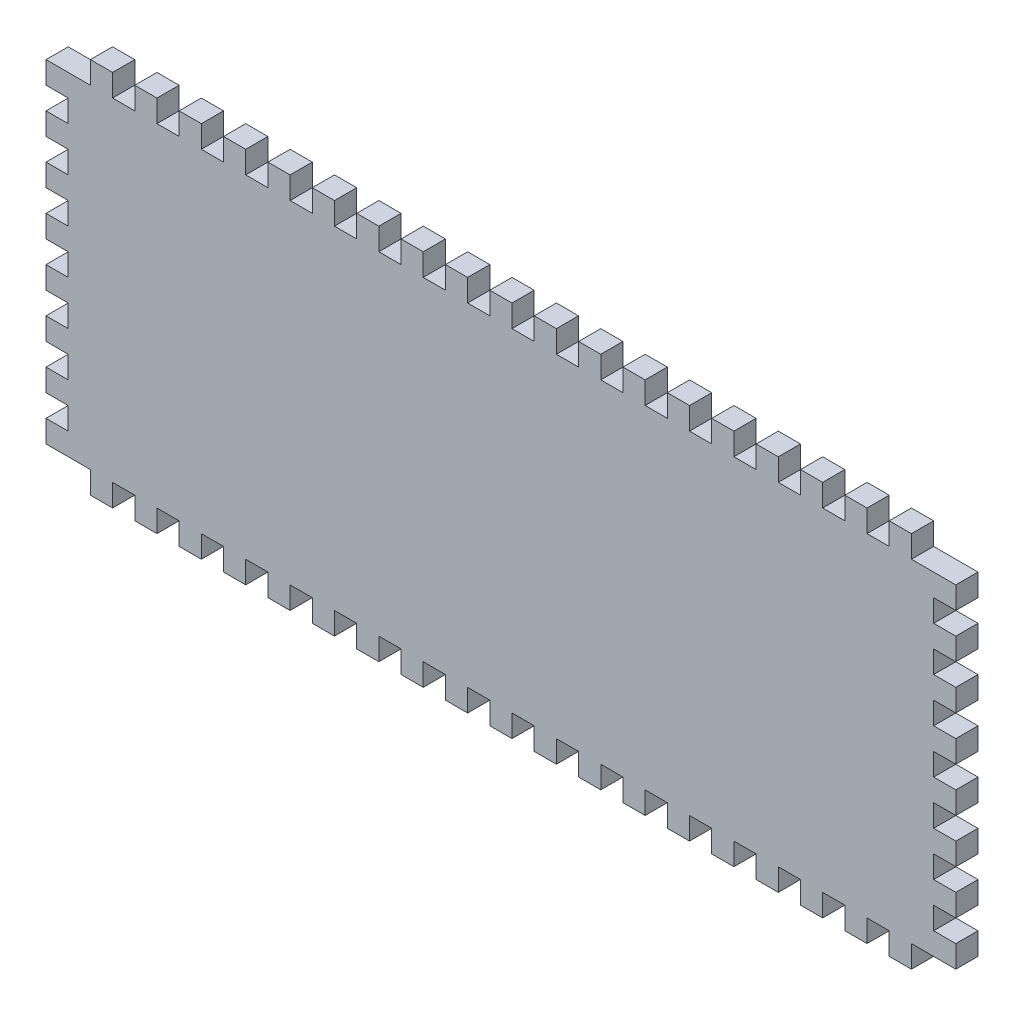
SolidWorks part; units mm, degrees
ref_plane "Front Plane" through (0, 0, 0) normal (0, 0, 1) x (1, 0, 0)
ref_plane "Top Plane" through (0, 0, 0) normal (0, 1, 0) x (1, 0, 0)
ref_plane "Right Plane" through (0, 0, 0) normal (1, 0, 0) x (0, 0, -1)
sketch "Sketch1" plane through (0, 0, 0) normal (0, 0, 1) x (1, 0, 0)
  line L1 (-130.175, -53.975) -> (130.175, -53.975)
  line L2 (-130.175, -53.975) -> (-130.175, 53.975)
  line L3 (-130.175, 53.975) -> (130.175, 53.975)
  line L4 (130.175, -53.975) -> (130.175, 53.975)
  line L5 (-130.175, -53.975) -> (130.175, 53.975) construction
  line L6 (-130.175, 53.975) -> (130.175, -53.975) construction
  point P0 (0, 0)
  dimension "D1" = 260.35
  dimension "D2" = 107.95
extrude "Boss-Extrude1" add sketch "Sketch1" along normal blind 6.35
sketch "Sketch3" plane through (0, 0, 6.35) normal (0, 0, 1) x (1, 0, 0)
  line L0 (-130.175, -53.975) -> (130.175, -53.975) construction
  line L1 (-123.825, -53.975) -> (-117.475, -53.975)
  line L2 (-123.825, -53.975) -> (-123.825, -47.625)
  line L3 (-123.825, -47.625) -> (-117.475, -47.625)
  line L4 (-117.475, -53.975) -> (-117.475, -47.625)
  dimension "D1" = 6.35
  dimension "D2" = 6.35
  dimension "D3" = 6.35
extrude "Cut-Extrude1" cut sketch "Sketch3" against normal through all
pattern_linear "LPattern1" count 20 spacing 12.7 along (1, 0, 0) of "Cut-Extrude1"
mirror "Mirror1" about plane through (0, 0, 0) normal (0, 1, 0) of "LPattern1", "Cut-Extrude1"
sketch "Sketch4" plane through (0, 0, 6.35) normal (0, 0, 1) x (1, 0, 0)
  line L1 (-130.175, -53.975) -> (-123.825, -53.975)
  line L2 (-130.175, -53.975) -> (-130.175, -47.625)
  line L3 (-130.175, -47.625) -> (-123.825, -47.625)
  line L4 (-123.825, -53.975) -> (-123.825, -47.625)
extrude "Cut-Extrude2" cut sketch "Sketch4" against normal through all
pattern_linear "LPattern3" count 9 spacing 12.7 along (0, 1, 0) of "Cut-Extrude2"
mirror "Mirror2" about plane through (0, 0, 0) normal (1, 0, 0) of "LPattern3", "Cut-Extrude2"
